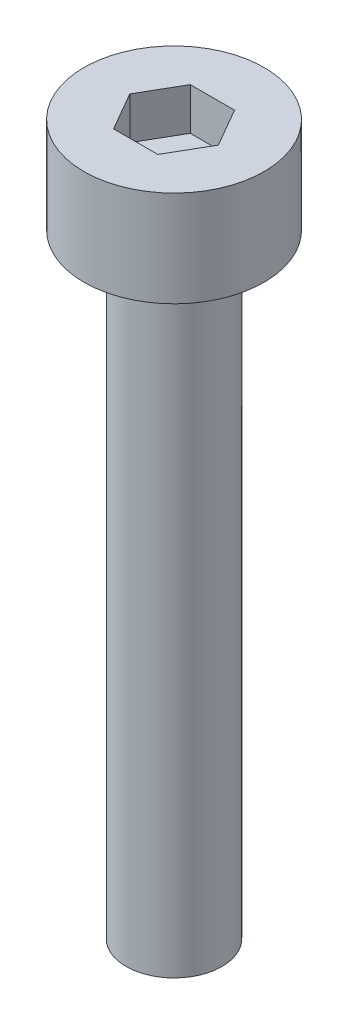
SolidWorks part; units mm, degrees
material "AISI 304"
ref_plane "前视基准面" through (0, 0, 0) normal (0, 0, 1) x (1, 0, 0)
ref_plane "上视基准面" through (0, 0, 0) normal (0, 1, 0) x (1, 0, 0)
ref_plane "右视基准面" through (0, 0, 0) normal (1, 0, 0) x (0, 0, -1)
sketch "草图1" plane through (0, 0, 0) normal (0, 1, 0) x (1, 0, 0)
  circle A0 centre (0, 0) radius 2.35
  dimension "D1" = 4.7
extrude "杯头" add sketch "草图1" along normal blind 2.5
sketch "草图2" plane through (0, 2.5, 0) normal (0, 1, 0) x (1, 0, 0)
  line L1 (1.1547, 0) -> (0.5774, 1)
  line L2 (0.5774, 1) -> (-0.5774, 1)
  line L3 (-0.5774, 1) -> (-1.1547, 0)
  line L4 (-1.1547, 0) -> (-0.5774, -1)
  line L5 (-0.5774, -1) -> (0.5774, -1)
  line L6 (0.5774, -1) -> (1.1547, 0)
  circle A0 centre (0, 0) radius 1 construction
  dimension "D1" = 2
extrude "内六角口" cut sketch "草图2" against normal blind 1.1
sketch "草图3" plane through (0, 0, 0) normal (0, -1, 0) x (1, 0, 0)
  circle A0 centre (0, 0) radius 1.25
  dimension "D1" = 2.5
extrude "螺纹长" add sketch "草图3" along normal blind 16
